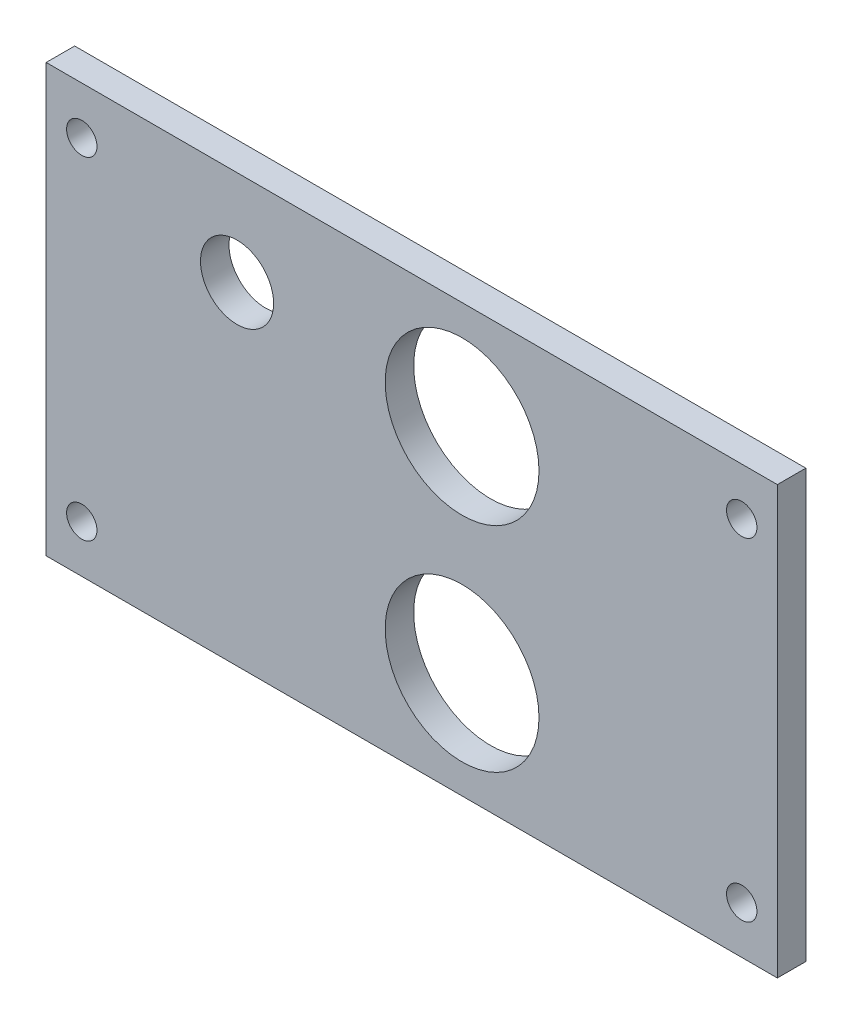
SolidWorks part; units mm, degrees
ref_plane "Alzado" through (0, 0, 0) normal (0, 0, 1) x (1, 0, 0)
ref_plane "Planta" through (0, 0, 0) normal (0, 1, 0) x (1, 0, 0)
ref_plane "Vista lateral" through (0, 0, 0) normal (1, 0, 0) x (0, 0, -1)
sketch "Croquis1" plane through (0, 0, 0) normal (0, 0, 1) x (1, 0, 0)
  line L1 (38.5, -22.5) -> (-38.5, -22.5)
  line L2 (38.5, -22.5) -> (38.5, 22.5)
  line L3 (38.5, 22.5) -> (-38.5, 22.5)
  line L4 (-38.5, -22.5) -> (-38.5, 22.5)
  line L5 (38.5, -22.5) -> (-38.5, 22.5) construction
  line L6 (38.5, 22.5) -> (-38.5, -22.5) construction
  point P0 (0, 0)
  dimension "D1" = 77
  dimension "D2" = 45
extrude "Saliente-Extruir1" add sketch "Croquis1" along normal blind 3
sketch "Croquis2" plane through (0, 0, 3) normal (0, 0, 1) x (1, 0, 0)
  line L0 (-34.75, -17.5) -> (-38.5, -17.5) construction
  line L1 (-34.75, 17.5) -> (34.75, 17.5) construction
  line L2 (-34.75, 17.5) -> (-34.75, -17.5) construction
  line L3 (-34.75, -17.5) -> (34.75, -17.5) construction
  line L4 (34.75, 17.5) -> (34.75, -17.5) construction
  line L5 (-38.5, 22.5) -> (-38.5, -22.5) construction
  line L6 (-34.75, -17.5) -> (-34.75, -22.5) construction
  line L7 (-38.5, -22.5) -> (38.5, -22.5) construction
  line L8 (34.75, 17.5) -> (34.75, 22.5) construction
  line L9 (38.5, 22.5) -> (-38.5, 22.5) construction
  line L10 (34.75, 17.5) -> (38.5, 17.5) construction
  line L11 (38.5, -22.5) -> (38.5, 22.5) construction
  circle A0 centre (5.3, 11.2) radius 8.1
  circle A1 centre (5.3, -11.3) radius 8.1
  circle A2 centre (-18.4, 12.5) radius 3.85
  circle A3 centre (-34.75, 17.5) radius 1.6
  circle A4 centre (34.75, 17.5) radius 1.6
  circle A5 centre (34.75, -17.5) radius 1.6
  circle A6 centre (-34.75, -17.5) radius 1.6
  dimension "D1" = 16.2
  dimension "D5" = 3.2
  dimension "D8" = 7.7
  dimension "D9" = 10
  dimension "D2" = 22.5
  dimension "D3" = 69.5
  dimension "D4" = 35
  dimension "D6" = 33.2
  dimension "D7" = 11.3
  dimension "D10" = 20.1
extrude "Cortar-Extruir1" cut sketch "Croquis2" against normal up to next
